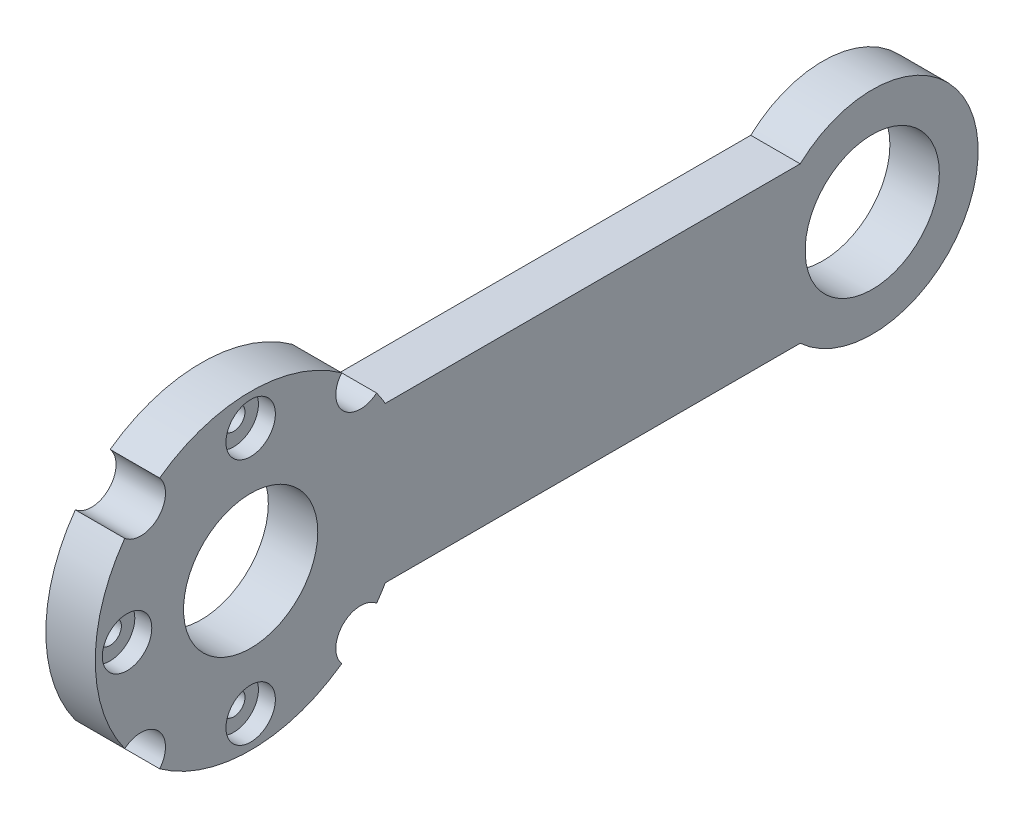
SolidWorks part; units mm, degrees
ref_plane "Front Plane" through (0, 0, 0) normal (0, 0, 1) x (1, 0, 0)
ref_plane "Top Plane" through (0, 0, 0) normal (0, 1, 0) x (1, 0, 0)
ref_plane "Right Plane" through (0, 0, 0) normal (1, 0, 0) x (0, 0, -1)
sketch "Sketch1" plane through (0, 0, 0) normal (1, 0, 0) x (0, 0, -1)
  line L1 (0, -11) -> (88, -11)
  line L2 (0, -11) -> (0, 11)
  line L3 (0, 11) -> (88, 11)
  line L4 (88, -11) -> (88, 11)
  circle A0 centre (0, 0) radius 17.5 construction
  circle A1 centre (0, 0) radius 22
  circle A2 centre (88, 0) radius 15
  dimension "D1" = 35
  dimension "D2" = 44
  dimension "D4" = 11
  dimension "D6" = 30
  dimension "D3" = 22
  dimension "D5" = 88
extrude "Boss-Extrude1" add sketch "Sketch1" along normal blind 7 contours L1 A2 L3 L4 | L3 A2 L1 L4 | A2 L3 A1 L1 | L3 A1 L1 L2 | L1 A1 L3 L2
sketch "Sketch3" plane through (7, 0, 0) normal (1, 0, 0) x (0, 0, -1)
  circle A0 centre (0, 0) radius 17.5 construction
  point P12 (0, 17.5)
  point P14 (-17.5, 0)
  point P16 (0, -17.5)
  dimension "D1" = 35
hole_wizard "CBORE for M3 Pan Head Machine Screw1" positions "Sketch3" profile "Sketch4" counterbore size "M3" standard "ANSI Metric" end condition through all
sketch "Sketch4" plane through (7, -17.5, 0) normal (0, 1, 0) x (0, 0, -1)
  line L0 (0, 0) -> (0, 7)
  line L1 (0, 7) -> (1.6, 7)
  line L3 (1.6, 7) -> (1.6, 2.4)
  line L4 (1.6, 2.4) -> (3.5, 2.4)
  line L5 (3.5, 2.4) -> (3.5, 0)
  line L7 (3.5, 0) -> (0, 0)
  line L11 (0, -6.35) -> (0, 107.95) construction
  dimension "Thru Hole Dia." = 3.2
  dimension "Thru Hole Depth" = 7
  dimension "C'Bore Dia." = 7
  dimension "C'Bore Depth" = 2.4
sketch "Sketch5" plane through (7, 0, 0) normal (1, 0, 0) x (0, 0, -1)
  circle A0 centre (0, 0) radius 9.5
  dimension "D1" = 19
extrude "Cut-Extrude1" cut sketch "Sketch5" against normal through all both and the other way through all
sketch "Sketch6" plane through (7, 0, 0) normal (1, 0, 0) x (0, 0, -1)
  line L0 (0, 0) -> (0, 22) construction
  line L1 (0, 22) -> (0, -22) construction
  line L2 (0, -22) -> (-21.9963, 0.4012) construction
  line L3 (-21.9963, 0.4012) -> (0, 22) construction
  line L4 (0, -22) -> (21.9963, -0.4012) construction
  line L5 (21.9963, -0.4012) -> (0, 22) construction
  line L6 (-21.6024, 0) -> (21.9963, -0.4012) construction
  line L7 (0, 0) -> (15.5563, 15.5563) construction
  line L8 (15.5563, 15.5563) -> (-15.5563, -15.5563) construction
  line L9 (-15.5563, -15.5563) -> (15.5563, -15.5563) construction
  line L10 (15.5563, -15.5563) -> (-15.5563, 15.5563) construction
  arc A0 (19.0526, 11) -> (19.0526, -11) centre (0, 0) ccw construction
  circle A1 centre (15.5563, 15.5563) radius 3.5
  circle A2 centre (-15.5563, 15.5563) radius 3.5
  circle A3 centre (-15.5563, -15.5563) radius 3.5
  circle A4 centre (15.5563, -15.5563) radius 3.5
  dimension "D1" = 7
extrude "Cut-Extrude2" cut sketch "Sketch6" against normal through all both and the other way through all
sketch "Sketch7" plane through (7, 0, 0) normal (1, 0, 0) x (0, 0, -1)
  circle A0 centre (88, 0) radius 9.5
  dimension "D1" = 19
extrude "Cut-Extrude3" cut sketch "Sketch7" against normal through all both and the other way through all
